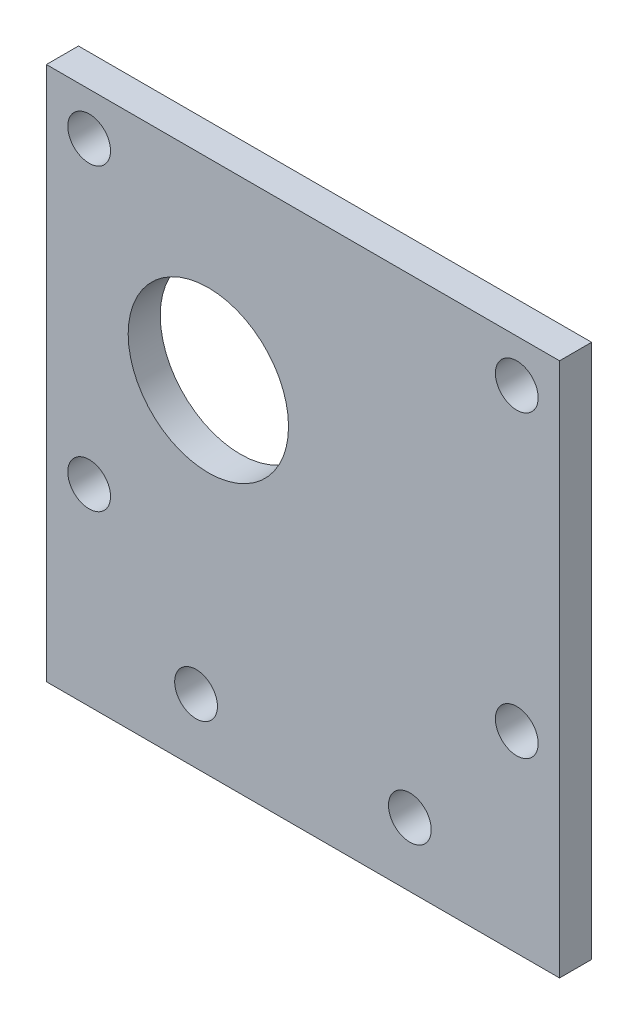
SolidWorks part; units mm, degrees
ref_plane "Front Plane" through (0, 0, 0) normal (0, 0, 1) x (1, 0, 0)
ref_plane "Top Plane" through (0, 0, 0) normal (0, 1, 0) x (1, 0, 0)
ref_plane "Right Plane" through (0, 0, 0) normal (1, 0, 0) x (0, 0, -1)
sketch "Sketch2" plane through (0, 0, 0) normal (0, 0, 1) x (1, 0, 0)
  line L0 (24, 50) -> (24, 0) construction
  line L1 (0, 0) -> (48, 0)
  line L2 (0, 0) -> (0, 50)
  line L3 (0, 50) -> (48, 50)
  line L4 (48, 0) -> (48, 50)
  circle A0 centre (4, 46) radius 2
  circle A1 centre (44, 46) radius 2
  circle A2 centre (44, 18) radius 2
  circle A3 centre (4, 18) radius 2
  circle A4 centre (15.15, 32) radius 7.5
  circle A5 centre (14, 6) radius 2
  circle A6 centre (34, 6) radius 2
  dimension "D3" = 4
  dimension "D8" = 15
  dimension "D13" = 4
  dimension "D14" = 4
  dimension "D1" = 48
  dimension "D2" = 50
  dimension "D4" = 20
  dimension "D5" = 20
  dimension "D6" = 28
  dimension "D7" = 28.85
  dimension "D9" = 14
  dimension "D10" = 4
  dimension "D11" = 6
  dimension "D12" = 6
  dimension "D15" = 10
  dimension "D16" = 10
extrude "Boss-Extrude2" add sketch "Sketch2" along normal blind 3
